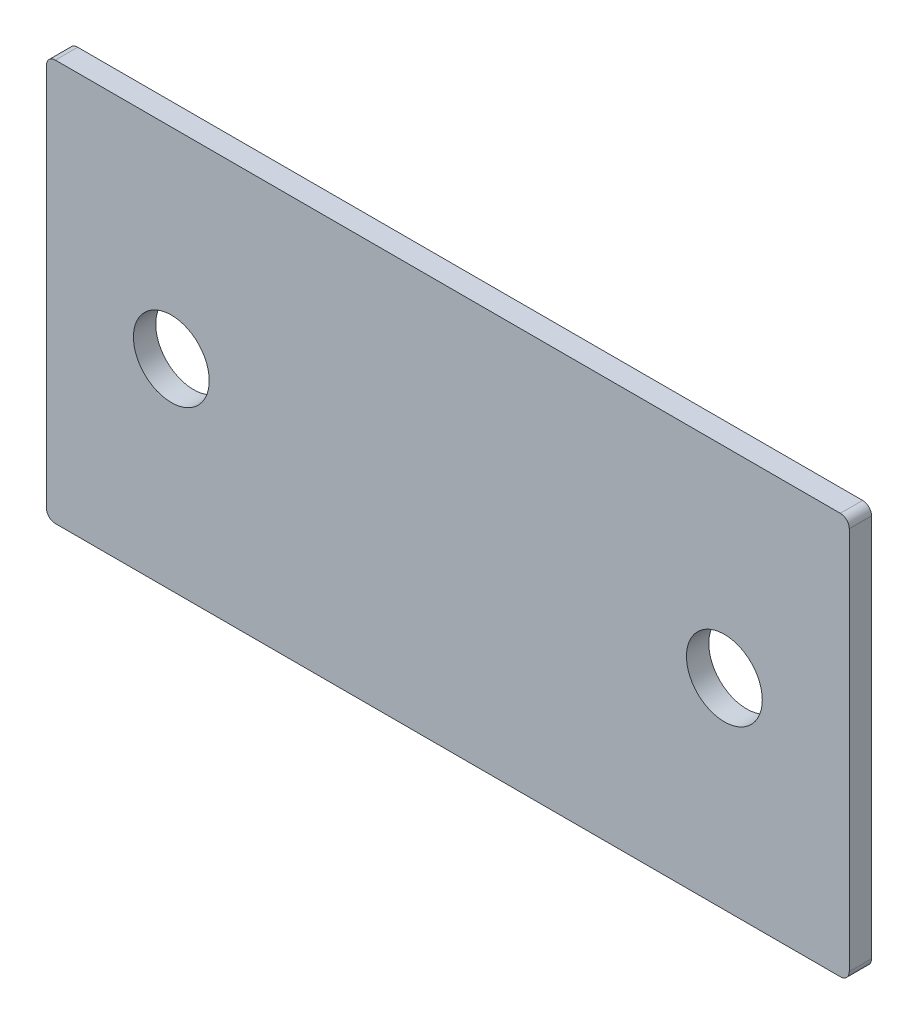
SolidWorks part; units mm, degrees
ref_plane "Спереди" through (0, 0, 0) normal (0, 0, 1) x (1, 0, 0)
ref_plane "Сверху" through (0, 0, 0) normal (0, 1, 0) x (1, 0, 0)
ref_plane "Справа" through (0, 0, 0) normal (1, 0, 0) x (0, 0, -1)
sketch "Эскиз1" plane through (0, 0, 0) normal (0, 0, 1) x (1, 0, 0)
  line L5 (-31, 0) -> (31, 0) construction
  line L6 (-45, -22.5) -> (45, -22.5)
  line L11 (-45, -22.5) -> (-45, 22.5)
  line L12 (-45, 22.5) -> (45, 22.5)
  line L16 (45, -22.5) -> (45, 22.5)
  line L17 (-45, -22.5) -> (45, 22.5) construction
  line L18 (-45, 22.5) -> (45, -22.5) construction
  circle A6 centre (-31, 0) radius 4.25
  circle A7 centre (31, 0) radius 4.25
  point P0 (0, 0)
  dimension "D4" = 8.5
  dimension "D3" = 14
  dimension "D1" = 90
  dimension "D2" = 45
extrude "Бобышка-Вытянуть1" add sketch "Эскиз1" along normal blind 2.5
fillet "Скругление1" radius 1 4 edges at (-45, -22.5, 1.25) (-45, 22.5, 1.25) (45, -22.5, 1.25) (45, 22.5, 1.25)
